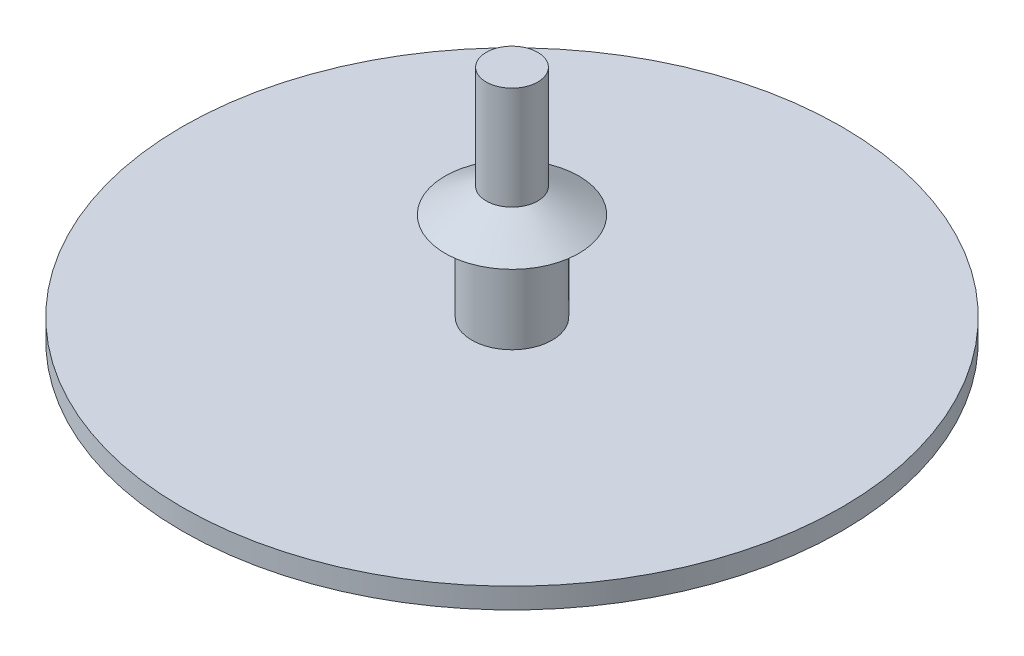
SolidWorks part; units mm, degrees
ref_plane "Front" through (0, 0, 0) normal (0, 0, 1) x (1, 0, 0)
ref_plane "Top" through (0, 0, 0) normal (0, 1, 0) x (1, 0, 0)
ref_plane "Right" through (0, 0, 0) normal (1, 0, 0) x (0, 0, -1)
sketch "Sketch1" plane through (0, 0, 0) normal (0, 0, 1) x (1, 0, 0)
  line L0 (1.95, 0.5) -> (1.95, 4.8)
  line L1 (0, -0.5) -> (16, -0.5)
  line L4 (16, -0.5) -> (16, 0.5)
  line L5 (0, 0) -> (16, 0.5) construction
  line L6 (0, 0) -> (16, -0.5) construction
  line L7 (1.95, 4.8) -> (3.25, 4.8)
  line L8 (3.25, 4.8) -> (1.25, 6)
  line L9 (1.25, 6) -> (1.25, 11)
  line L10 (1.25, 11) -> (0, 11)
  line L11 (0, 11) -> (0, -0.5)
  line L12 (0, 0) -> (0, 13.0257) construction
  line L13 (1.95, 0.5) -> (16, 0.5)
  point P0 (0, 0)
  point P8 (0, 13.0257)
  dimension "D2" = 1
  dimension "D3" = 3.9
  dimension "D5" = 6.5
  dimension "D7" = 5
  dimension "D8" = 2.5
revolve "Revolve1" add sketch "Sketch1" angle 360 about L12
